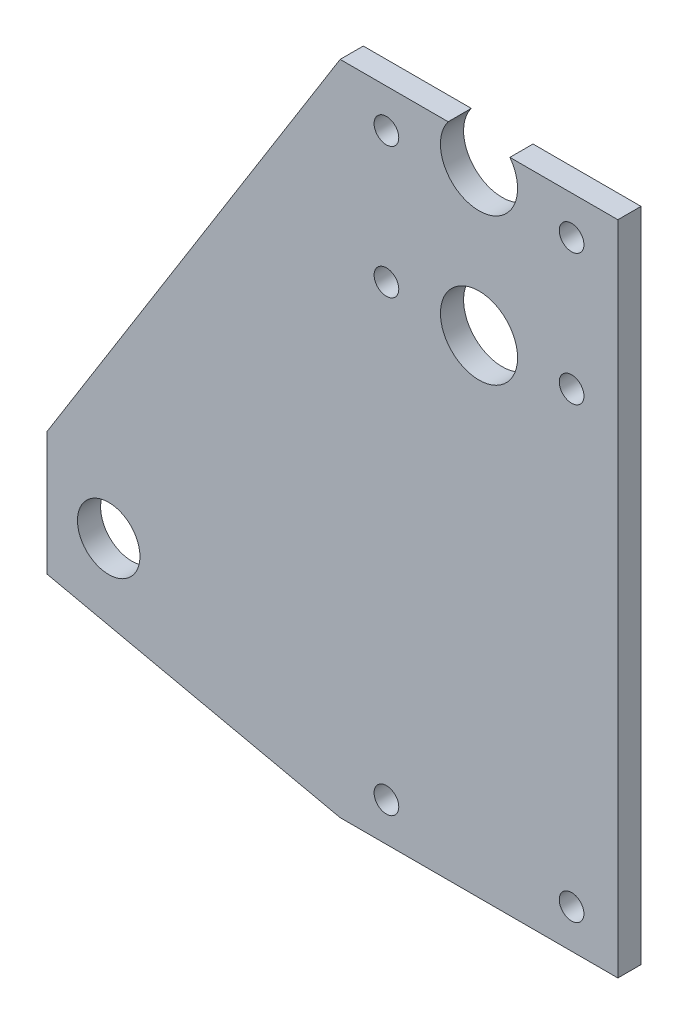
SolidWorks part; units mm, degrees
ref_plane "正面" through (0, 0, 0) normal (0, 0, 1) x (1, 0, 0)
ref_plane "平面" through (0, 0, 0) normal (0, 1, 0) x (1, 0, 0)
ref_plane "右側面" through (0, 0, 0) normal (1, 0, 0) x (0, 0, -1)
sketch "ｽｹｯﾁ1" plane through (0, 0, 0) normal (0, 0, 1) x (1, 0, 0)
  line L0 (74, 98.7795) -> (38, 98.7795)
  line L1 (38, 98.7795) -> (0, 38)
  line L2 (0, 46) -> (0, 0) construction
  line L3 (0, 38) -> (0, 22)
  line L4 (0, 22) -> (38, 13.6572)
  line L5 (38, 13.6572) -> (74, 13.6572)
  line L8 (74, 13.6572) -> (74, 98.7795)
  line L9 (38, 13.6572) -> (38, 23.6572) construction
  circle A0 centre (68, 93.7795) radius 1.6
  circle A1 centre (68, 76.7795) radius 1.6
  circle A2 centre (44, 93.7795) radius 1.6
  circle A3 centre (44, 76.7795) radius 1.6
  circle A4 centre (68, 18.6572) radius 1.6
  circle A5 centre (44, 18.6572) radius 1.6
  circle A6 centre (8, 30) radius 4.05
  arc A7 (52, 98.7795) -> (60, 98.7795) centre (56, 95.7795) ccw
  circle A8 centre (56, 76.7795) radius 5
  point P14 (0, 30)
  point P35 (38, 18.6572)
  point P40 (56, 98.7795)
  dimension "D1" = 3.2
  dimension "D2" = 8.1
  dimension "D4" = 19
  dimension "D5" = 10
  dimension "D3" = 3
extrude "ﾎﾞｽ - 押し出し1" add sketch "ｽｹｯﾁ1" against normal blind 3 contours A7 L0 L1 L3 L4 L5 L8 A8 A6 A5 A4 A3 A2 A1 A0
